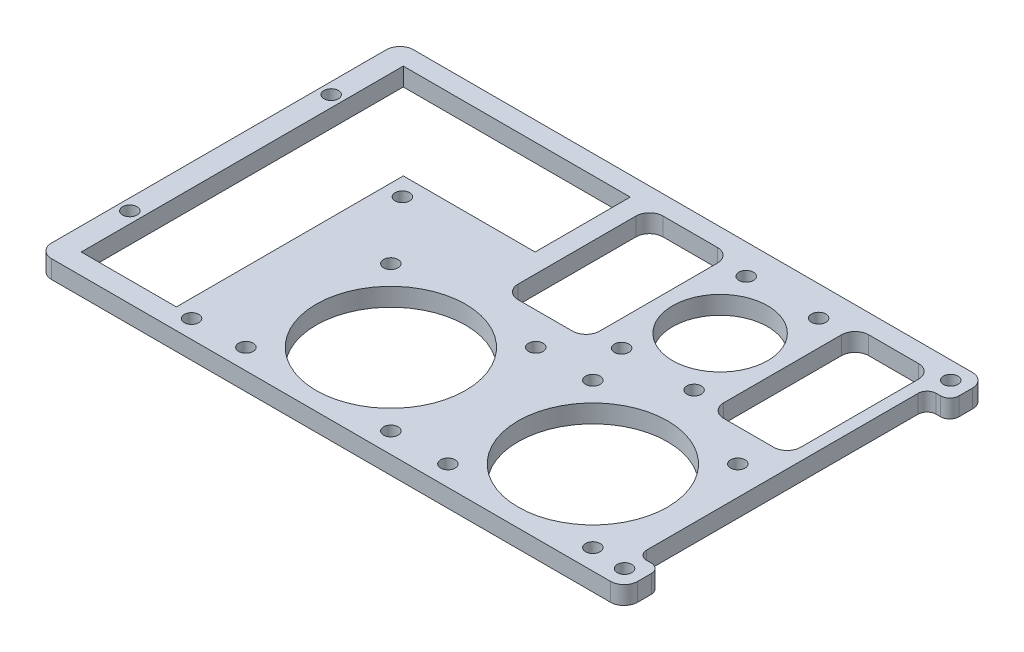
SolidWorks part; units mm, degrees
ref_plane "Front Plane" through (0, 0, 0) normal (0, 0, 1) x (1, 0, 0)
ref_plane "Top Plane" through (0, 0, 0) normal (0, 1, 0) x (1, 0, 0)
ref_plane "Right Plane" through (0, 0, 0) normal (1, 0, 0) x (0, 0, -1)
sketch "Sketch1" plane through (0, 0, 0) normal (0, 1, 0) x (1, 0, 0)
  line L0 (0, 0) -> (129.4, 0)
  line L1 (129.4, 0) -> (129.4, 79.9)
  line L2 (129.4, 79.9) -> (0, 79.9)
  line L3 (0, 79.9) -> (0, 0)
  dimension "D1" = 79.9
  dimension "D2" = 129.4
extrude "Boss-Extrude1" add sketch "Sketch1" along normal blind 4
fillet "Fillet1" radius 3 4 edges at (0, 2, -79.9) (0, 2, 0) (129.4, 2, -79.9) (129.4, 2, 0)
sketch "Sketch2" plane through (0, 4, 0) normal (0, 1, 0) x (1, 0, 0)
  line L0 (5, 4.55) -> (26, 4.55)
  line L2 (26, 4.55) -> (26, 54.65)
  line L3 (55.1, 54.65) -> (26, 54.65)
  line L5 (5, 40) -> (5, 4.55)
  line L6 (5, 40) -> (5, 75.65)
  line L7 (5, 75.65) -> (55.1, 75.65)
  line L9 (55.1, 75.65) -> (55.1, 54.65)
  line L10 (0, 76.9) -> (0, 3) construction
  dimension "D1" = 5
  dimension "D2" = 71.1
  dimension "D3" = 21
  dimension "D4" = 21
  dimension "D5" = 50.1
extrude "Cut-Extrude1" cut sketch "Sketch2" against normal blind 10
sketch "Sketch3" plane through (0, 4, 0) normal (0, 1, 0) x (1, 0, 0)
  line L0 (55.1, 75.65) -> (55.1, 79.05)
  line L1 (56, 79.05) -> (56, 40.05)
  line L2 (56, 40.05) -> (128, 40.05)
  line L3 (55.1, 79.05) -> (56, 79.05)
  line L4 (56, 79.05) -> (128, 79.05)
  line L5 (128, 79.05) -> (128, 40.05)
  line L6 (26, 4.55) -> (26, 0.95)
  line L7 (26, 0.95) -> (38.8, 0.95)
  line L8 (38.8, 0.95) -> (38.8, 40.05)
  line L9 (38.8, 40.05) -> (128, 40.05)
  line L10 (128, 40.05) -> (128, 0.95)
  line L11 (128, 0.95) -> (38.8, 0.95)
  circle A0 centre (99.05, 73.3) radius 1.6
  circle A1 centre (83.05, 73.3) radius 1.6
  circle A2 centre (99.05, 45.8) radius 1.6
  circle A3 centre (83.05, 45.8) radius 1.6
  circle A4 centre (91.05, 59.55) radius 10.5
  circle A5 centre (73.4, 36.5) radius 1.6
  circle A6 centre (41.4, 36.5) radius 1.6
  circle A7 centre (73.4, 4.5) radius 1.6
  circle A8 centre (41.4, 4.5) radius 1.6
  circle A9 centre (86, 36.5) radius 1.6
  circle A10 centre (118, 36.5) radius 1.6
  circle A11 centre (118, 4.5) radius 1.6
  circle A12 centre (86, 4.5) radius 1.6
  circle A13 centre (57.4, 20.5) radius 16.5
  circle A14 centre (102, 20.5) radius 16.5
extrude "Cut-Extrude2" cut sketch "Sketch3" against normal blind 10 contours A4 | A1 | A0 | A2 | A3 | A6 | A5 | A9 | A10 | A14 | A13 | A8 | A7 | A12 | A11
sketch "Sketch4" plane through (0, 4, 0) normal (0, 1, 0) x (1, 0, 0)
  circle A0 centre (125.5, 4) radius 1.6
  circle A1 centre (125.5, 76) radius 1.6
  circle A2 centre (29.9, 50.55) radius 1.6
  circle A3 centre (29.9, 4) radius 1.6
extrude "Cut-Extrude3" cut sketch "Sketch4" against normal blind 10
sketch "Sketch5" plane through (0, 4, 0) normal (0, 1, 0) x (1, 0, 0)
  line L0 (59.35, 75.65) -> (77.35, 75.65)
  line L1 (59.35, 43.65) -> (59.35, 75.65)
  line L2 (104.75, 75.65) -> (121.75, 75.65)
  line L3 (59.35, 43.65) -> (77.35, 43.65)
  line L4 (77.35, 43.65) -> (77.35, 75.65)
  line L7 (104.75, 75.65) -> (104.75, 43.65)
  line L8 (104.75, 43.65) -> (121.75, 43.65)
  line L9 (121.75, 43.65) -> (121.75, 75.65)
extrude "Cut-Extrude4" cut sketch "Sketch5" against normal blind 10
sketch "Sketch6" plane through (0, 4, 0) normal (0, 1, 0) x (1, 0, 0)
  line L1 (129.4, 3) -> (129.4, 76.9) construction
  line L2 (129.4, 71.9) -> (124.4, 71.9)
  line L4 (129.4, 8) -> (124.4, 8)
  line L5 (124.4, 8) -> (124.4, 71.9)
  line L6 (129.4, 71.9) -> (129.4, 8)
extrude "Cut-Extrude5" cut sketch "Sketch6" against normal blind 10
fillet "Fillet2" radius 2 4 edges at (129.4, 2, -8) (124.4, 2, -8) (124.4, 2, -71.9) (129.4, 2, -71.9)
sketch "Sketch7" plane through (0, 0, 0) normal (0, -1, 0) x (-1, 0, 0)
  circle A0 centre (-2.5, 17.775) radius 1.6
  circle A1 centre (-2.5, 62.225) radius 1.6
extrude "Cut-Extrude6" cut sketch "Sketch7" against normal blind 10
fillet "Fillet3" radius 3 8 edges at (104.75, 2, -43.65) (121.75, 2, -43.65) (121.75, 2, -75.65) (104.75, 2, -75.65) (59.35, 2, -75.65) (77.35, 2, -75.65) (77.35, 2, -43.65) (59.35, 2, -43.65)
